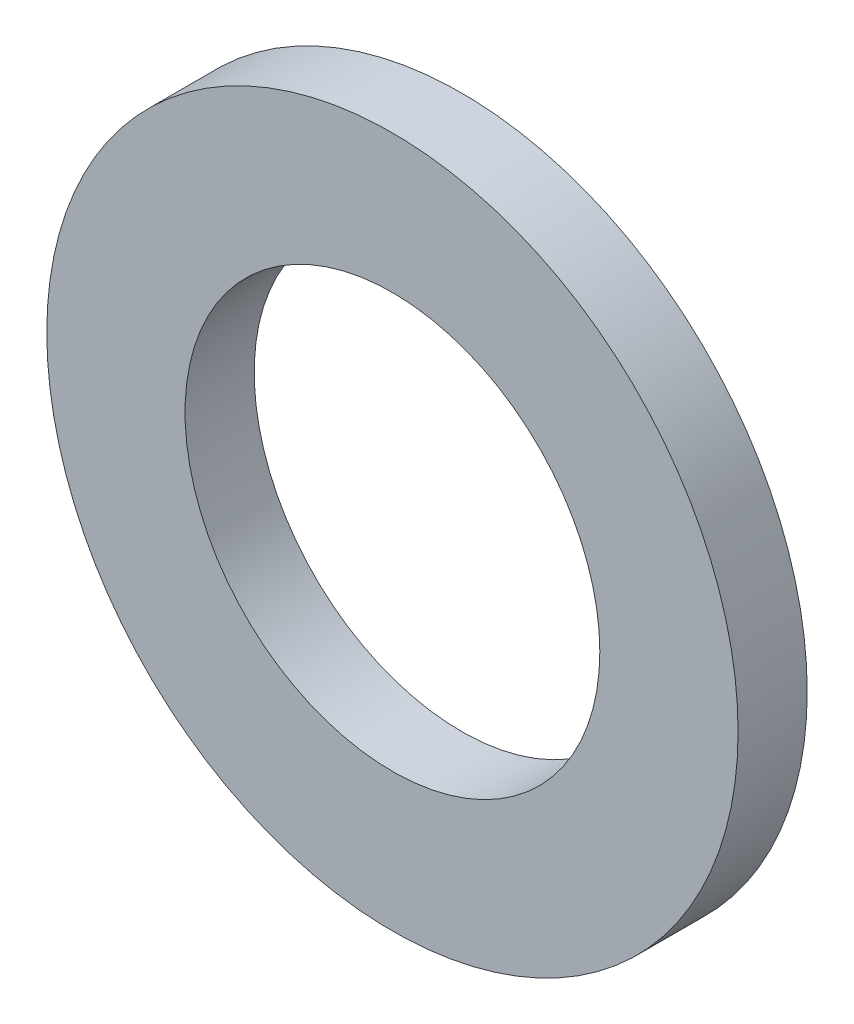
SolidWorks part; units mm, degrees
ref_plane "前视基准面" through (0, 0, 0) normal (0, 0, 1) x (1, 0, 0)
ref_plane "上视基准面" through (0, 0, 0) normal (0, 1, 0) x (1, 0, 0)
ref_plane "右视基准面" through (0, 0, 0) normal (1, 0, 0) x (0, 0, -1)
sketch "草图1" plane through (0, 0, 0) normal (0, 0, 1) x (1, 0, 0)
  circle A0 centre (0, 0) radius 1.5
  circle A1 centre (0, 0) radius 2.5
  dimension "D1" = 3
  dimension "D2" = 5
extrude "凸台-拉伸1" add sketch "草图1" along normal mid plane 0.5
